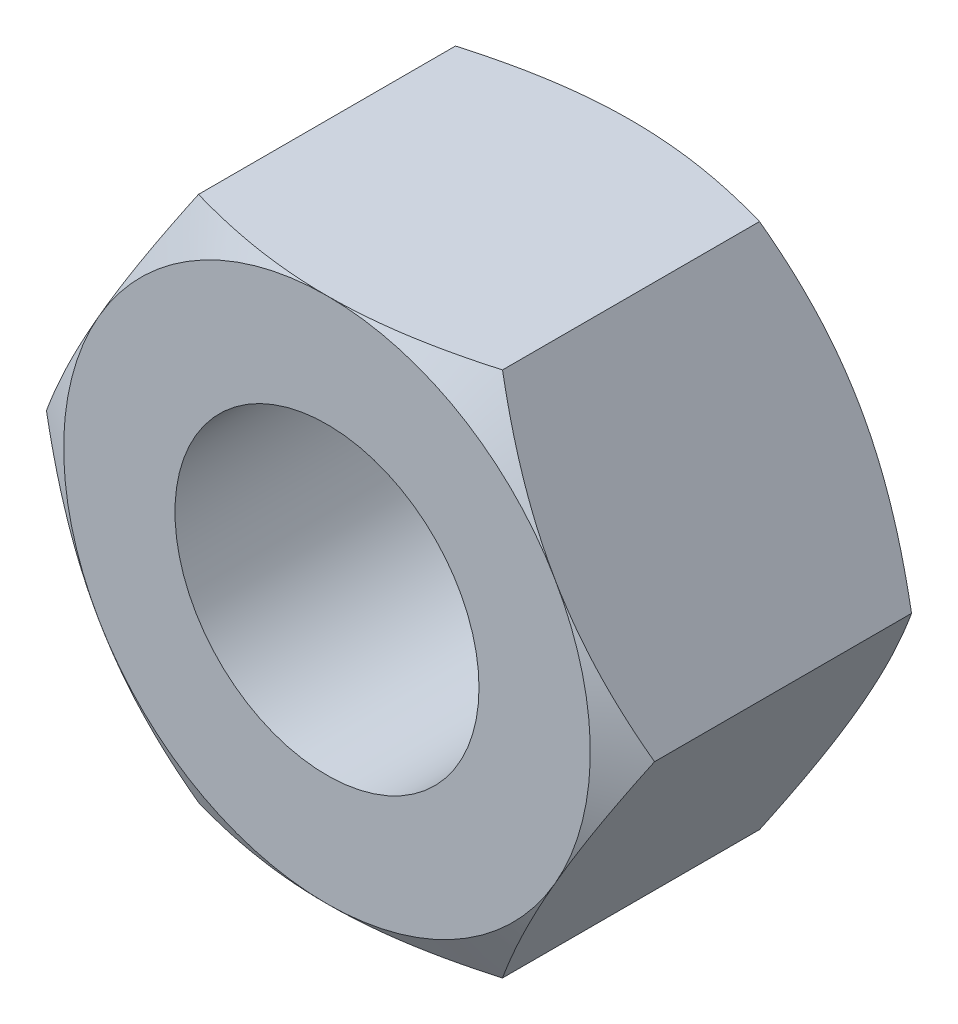
SolidWorks part; units mm, degrees
ref_plane "Front Plane" through (0, 0, 0) normal (0, 0, 1) x (1, 0, 0)
ref_plane "Top Plane" through (0, 0, 0) normal (0, 1, 0) x (1, 0, 0)
ref_plane "Right Plane" through (0, 0, 0) normal (1, 0, 0) x (0, 0, -1)
sketch "Sketch4" plane through (0, 0, 0) normal (0, 0, 1) x (1, 0, 0)
  line L1 (4.5, 7.7942) -> (-4.5, 7.7942)
  line L2 (-4.5, 7.7942) -> (-9, 0)
  line L3 (-9, 0) -> (-4.5, -7.7942)
  line L4 (-4.5, -7.7942) -> (4.5, -7.7942)
  line L5 (4.5, -7.7942) -> (9, 0)
  line L6 (9, 0) -> (4.5, 7.7942)
  circle A0 centre (0, 0) radius 7.7942 construction
  circle A1 centre (0, 0) radius 4.5
  dimension "D2" = 9
  dimension "D1" = 9
extrude "Boss-Extrude1" add sketch "Sketch4" along normal mid plane 9
sketch "Sketch5" plane through (0, 0, 4.5) normal (0, 0, 1) x (1, 0, 0)
  line L0 (9, 0) -> (4.5, 7.7942) construction
  circle A0 centre (0, 0) radius 7.7942
extrude "Cut-Extrude1" cut sketch "Sketch5" against normal blind 9 draft 60 flip side to cut
mirror "Mirror1" about plane through (0, 0, 0) normal (0, 0, 1) of "Cut-Extrude1"
